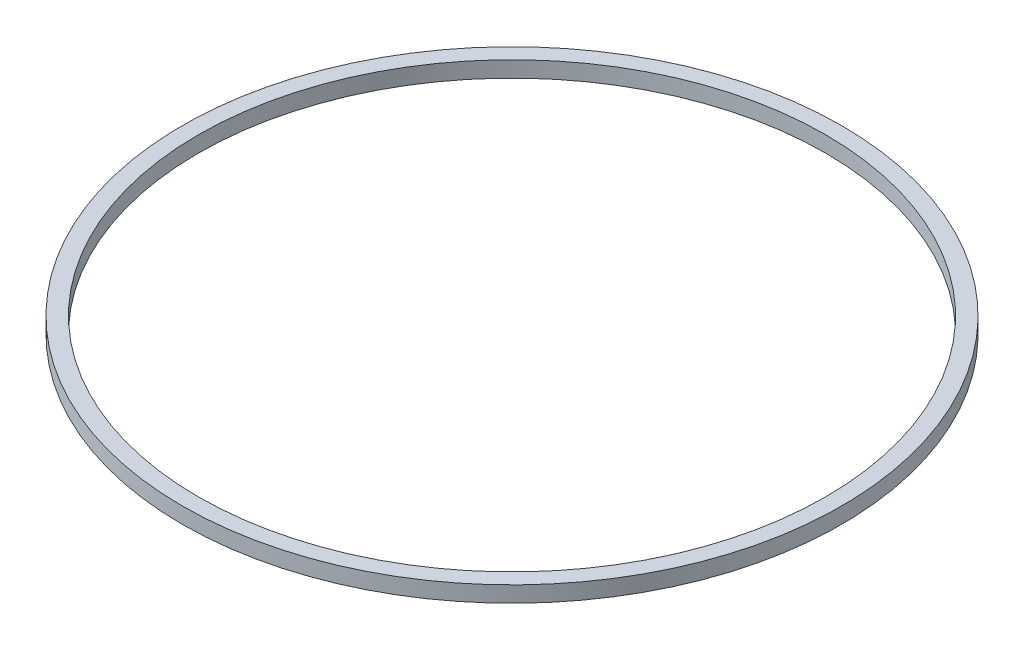
SolidWorks part; units mm, degrees
ref_plane "Front Plane" through (0, 0, 0) normal (0, 0, 1) x (1, 0, 0)
ref_plane "Top Plane" through (0, 0, 0) normal (0, 1, 0) x (1, 0, 0)
ref_plane "Right Plane" through (0, 0, 0) normal (1, 0, 0) x (0, 0, -1)
sketch "Sketch1" plane through (0, 0, 0) normal (0, 0, 1) x (1, 0, 0)
  line L1 (1500, 25.1354) -> (1576.2, 25.1354)
  line L2 (1500, 25.1354) -> (1500, -51.0646)
  line L3 (1500, -51.0646) -> (1576.2, -51.0646)
  line L4 (1576.2, 25.1354) -> (1576.2, -51.0646)
  line L5 (1500, 25.1354) -> (1576.2, -51.0646) construction
  line L6 (1500, -51.0646) -> (1576.2, 25.1354) construction
  point P0 (1538.1, -12.9646)
  dimension "D1" = 76.2
  dimension "D2" = 76.2
  dimension "D3" = 1500
ref_axis "Axis1" through (0, 0, 0) along (0, 1, 0)
revolve "Revolve1" add sketch "Sketch1" angle 360 about axis through (0, 0, 0) along (0, 1, 0)
